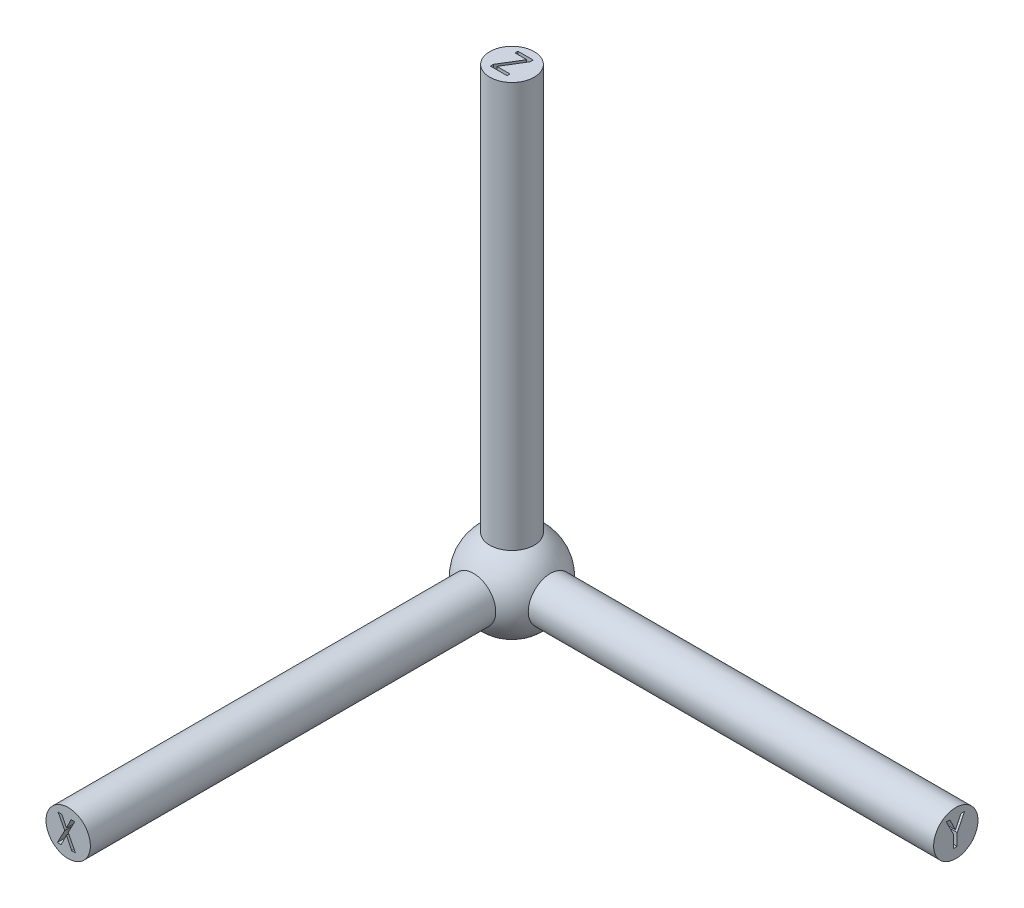
SolidWorks part; units mm, degrees
ref_plane "前视基准面" through (0, 0, 0) normal (0, 0, 1) x (1, 0, 0)
ref_plane "上视基准面" through (0, 0, 0) normal (0, 1, 0) x (1, 0, 0)
ref_plane "右视基准面" through (0, 0, 0) normal (1, 0, 0) x (0, 0, -1)
sketch "草图1" plane through (0, 0, 0) normal (0, 0, 1) x (1, 0, 0)
  line L0 (0, 1) -> (0, -1)
  arc A0 (0, 1) -> (0, -1) centre (0, 0) ccw
  point P4 (0, 0)
  dimension "D1" = 1
revolve "旋转1" add sketch "草图1" angle 360 about L0
sketch "草图2" plane through (0, 0, 0) normal (0, 1, 0) x (1, 0, 0)
  circle A0 centre (0, 0) radius 0.5
  dimension "D1" = 1
extrude "凸台-拉伸1" add sketch "草图2" along normal blind 10
sketch "草图3" plane through (0, 0, 0) normal (1, 0, 0) x (0, 0, -1)
  circle A0 centre (0, 0) radius 0.5
  dimension "D1" = 1
extrude "凸台-拉伸2" add sketch "草图3" along normal blind 10
sketch "草图4" plane through (0, 0, 0) normal (0, 0, 1) x (1, 0, 0)
  circle A0 centre (0, 0) radius 0.5
  dimension "D1" = 1
extrude "凸台-拉伸3" add sketch "草图4" along normal blind 10
sketch "草图5" plane through (0, 0, 10) normal (0, 0, 1) x (1, 0, 0)
  text T0 "X" font "黑体" height 0.6
extrude "切除-拉伸1" cut sketch "草图5" against normal blind 1
sketch "草图6" plane through (10, 0, 0) normal (1, 0, 0) x (0, 0, -1)
  text T0 "Y" font "黑体" height 0.6
extrude "切除-拉伸2" cut sketch "草图6" against normal blind 1
sketch "草图7" plane through (0, 10, 0) normal (0, 1, 0) x (1, 0, 0)
  text T0 "Z" font "黑体" height 0.6
extrude "切除-拉伸3" cut sketch "草图7" against normal blind 1
